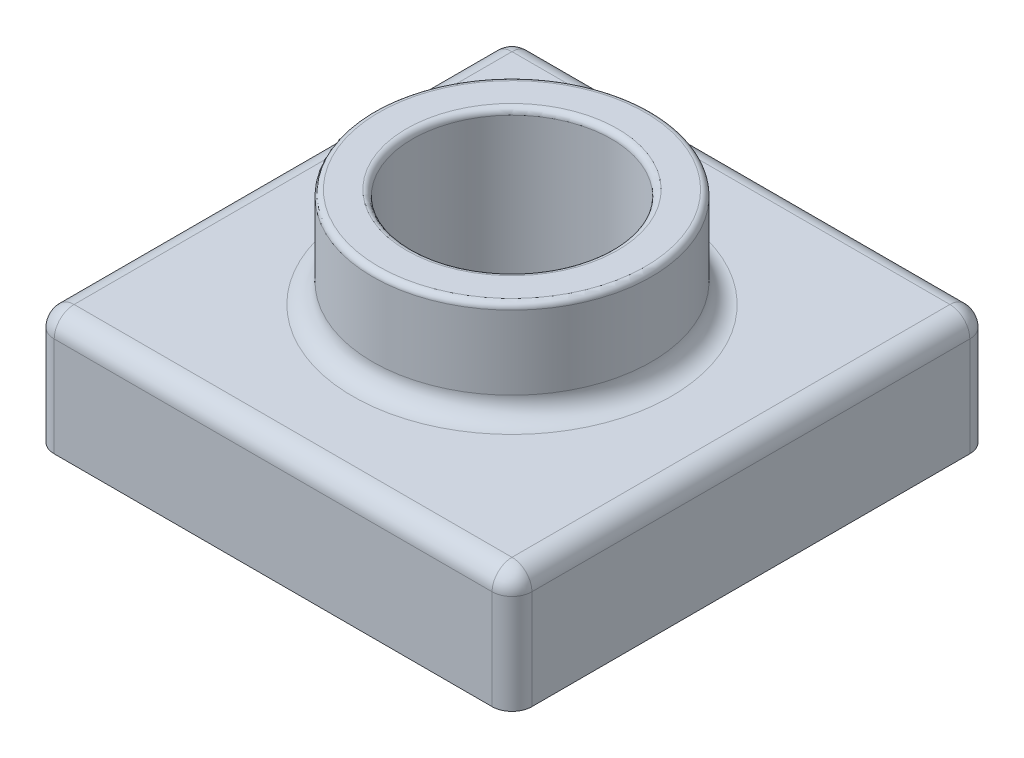
SolidWorks part; units mm, degrees
ref_plane "Front Plane" through (0, 0, 0) normal (0, 0, 1) x (1, 0, 0)
ref_plane "Top Plane" through (0, 0, 0) normal (0, 1, 0) x (1, 0, 0)
ref_plane "Right Plane" through (0, 0, 0) normal (1, 0, 0) x (0, 0, -1)
sketch "Sketch1" plane through (0, 0, 0) normal (0, 1, 0) x (1, 0, 0)
  line L1 (-60, -60) -> (60, -60)
  line L2 (-60, -60) -> (-60, 60)
  line L3 (-60, 60) -> (60, 60)
  line L4 (60, -60) -> (60, 60)
  line L5 (-60, -60) -> (60, 60) construction
  line L6 (-60, 60) -> (60, -60) construction
  point P0 (0, 0)
  dimension "D1" = 120
  dimension "D2" = 120
extrude "Boss-Extrude1" add sketch "Sketch1" along normal blind 30
sketch "Sketch2" plane through (0, 30, 0) normal (0, 1, 0) x (1, 0, 0)
  circle A0 centre (0, 0) radius 35
  dimension "D1" = 70
extrude "Boss-Extrude2" add sketch "Sketch2" along normal blind 25
sketch "Sketch3" plane through (0, 55, 0) normal (0, 1, 0) x (1, 0, 0)
  circle A0 centre (0, 0) radius 25
  dimension "D1" = 50
extrude "Cut-Extrude1" cut sketch "Sketch3" against normal through all
fillet "Fillet1" radius 5 9 edges at (0, 30, 35) (60, 15, 60) (-60, 15, 60) (-60, 30, 0) (0, 30, 60) (60, 15, -60) (60, 30, 0) (0, 30, -60) (-60, 15, -60)
fillet "Fillet2" radius 1.5 2 edges at (0, 55, 35) (0, 55, 25)
shell "Shell1" thickness 2
